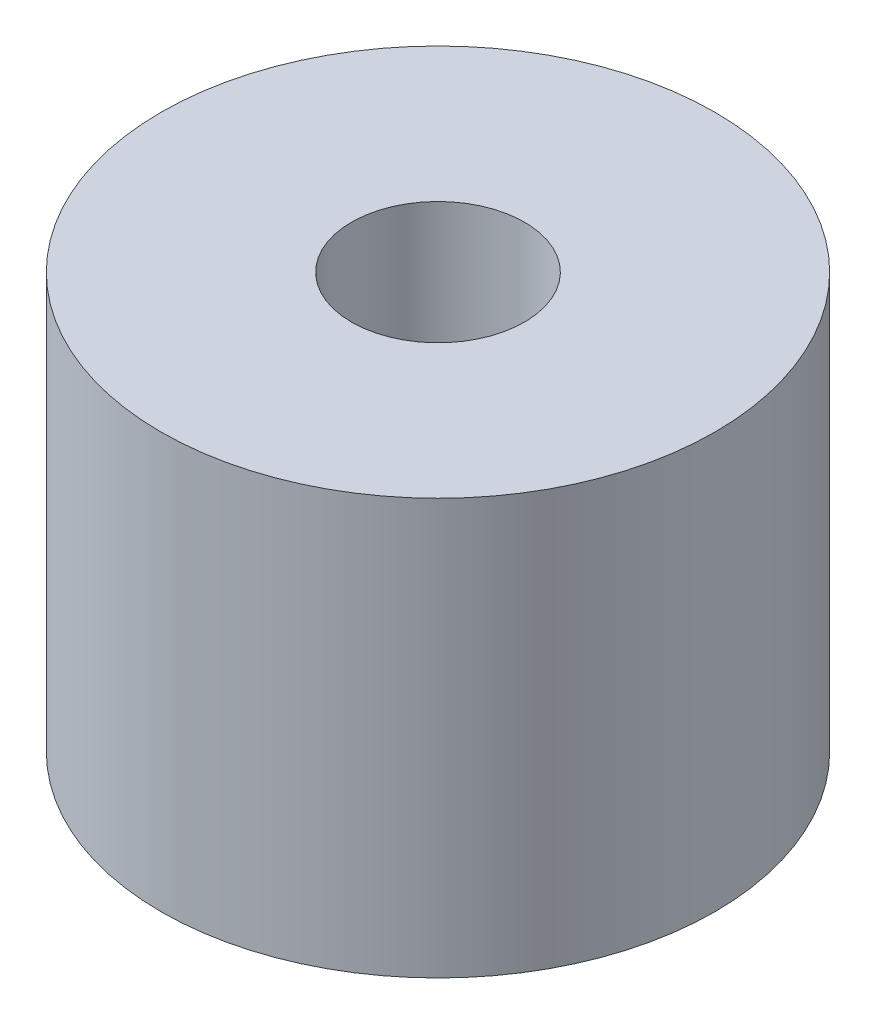
SolidWorks part; units mm, degrees
material "RBAR,1018CR"
ref_plane "Front Plane" through (0, 0, 0) normal (0, 0, 1) x (1, 0, 0)
ref_plane "Top Plane" through (0, 0, 0) normal (0, 1, 0) x (1, 0, 0)
ref_plane "Right Plane" through (0, 0, 0) normal (1, 0, 0) x (0, 0, -1)
sketch "Sketch1" plane through (0, 0, 0) normal (0, 1, 0) x (1, 0, 0)
  circle A0 centre (0, 0) radius 12.7
  dimension "D1" = 25.4
extrude "Boss-Extrude1" add sketch "Sketch1" along normal blind 19.05
hole_wizard "Tap Drill for 3/8-16 Tap1" positions "Sketch3" profile "Sketch2" hole size "3/8-16" standard "ANSI Inch" end condition through all
sketch "Sketch3" plane through (0, 19.05, 0) normal (0, 1, 0) x (1, 0, 0)
  point P0 (0, 0)
sketch "Sketch2" plane through (0, 19.05, 0) normal (1, 0, 0) x (0, 0, 1)
  line L0 (0, 0) -> (0, 19.05)
  line L1 (0, 19.05) -> (3.9687, 19.05)
  line L2 (3.9687, 19.05) -> (3.9687, 0)
  line L5 (3.9687, 0) -> (0, 0)
  line L11 (0, -6.35) -> (0, 107.95) construction
  dimension "Thru Hole Dia." = 7.9375
  dimension "Thru Hole Depth" = 19.05
hole_wizard "Tap Drill for 3/8-16 Tap2" positions "Sketch5" profile "Sketch4" hole size "3/8-16" standard "ANSI Inch"
sketch "Sketch5" plane through (0, 0, 0) normal (0, -1, 0) x (-1, 0, 0)
  point P0 (0, 0)
sketch "Sketch4" plane through (0, 0, 0) normal (1, 0, 0) x (0, 0, -1)
  line L0 (0, 0) -> (0, 22.9587)
  line L1 (0, 22.9587) -> (3.9687, 20.574)
  line L2 (3.9687, 20.574) -> (3.9687, 0)
  line L5 (3.9687, 0) -> (0, 0)
  line L10 (0, 22.9587) -> (-3.9688, 20.574) construction
  line L11 (0, -6.35) -> (0, 107.95) construction
  dimension "Hole Dia." = 7.9375
  dimension "Hole Depth" = 20.574
  dimension "Drill Angle" = 118
